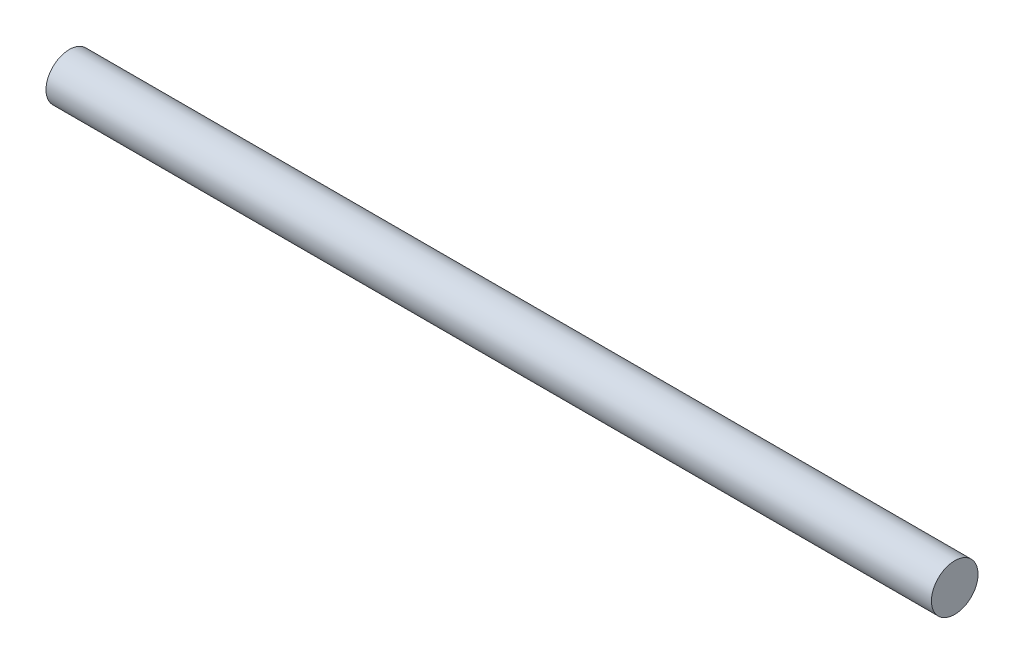
SolidWorks part; units mm, degrees
ref_plane "Front Plane" through (0, 0, 0) normal (0, 0, 1) x (1, 0, 0)
ref_plane "Top Plane" through (0, 0, 0) normal (0, 1, 0) x (1, 0, 0)
ref_plane "Right Plane" through (0, 0, 0) normal (1, 0, 0) x (0, 0, -1)
sketch "Sketch1" plane through (0, 0, 0) normal (0, 0, 1) x (1, 0, 0)
  line L0 (-47.5, 2.5) -> (47.5, 2.5)
  line L1 (0, -55) -> (0, 55) construction
  line L2 (55, 0) -> (-55, 0) construction
  line L3 (-9.1355, 0) -> (10.8257, 0) construction
  line L4 (47.5, 2.5) -> (47.5, 0)
  line L5 (-47.5, 2.5) -> (-47.5, 0)
  line L6 (47.5, 0) -> (-47.5, 0)
  point P2 (0, 2.5)
  dimension "D1" = 95
  dimension "D2" = 2.5
revolve "Revolve1" add sketch "Sketch1" angle 360 about L3
